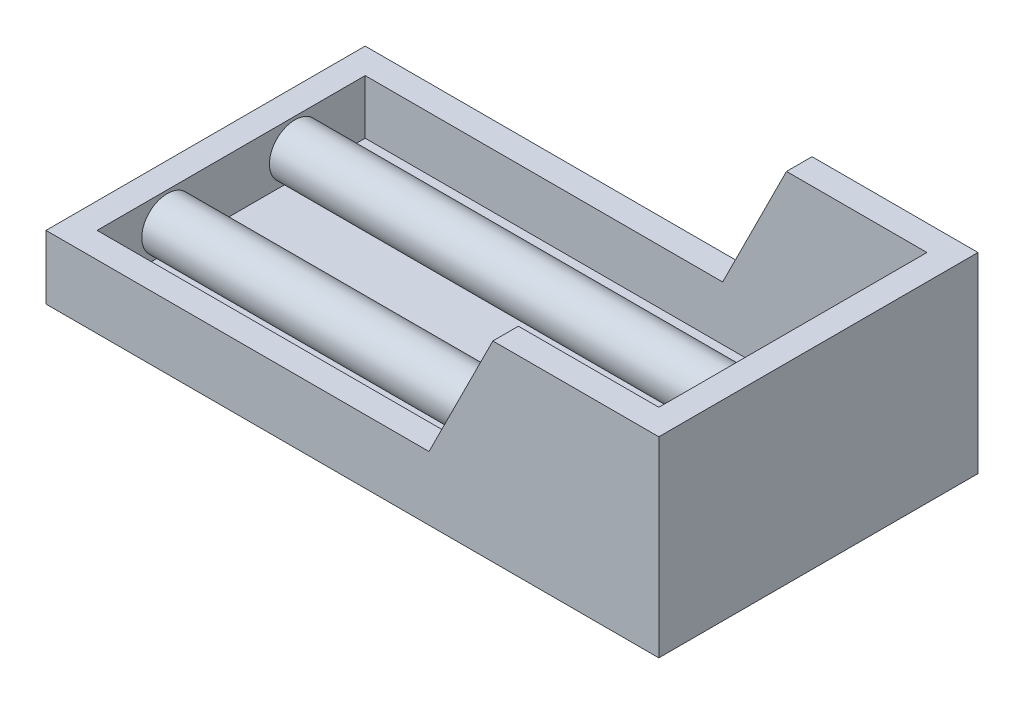
SolidWorks part; units mm, degrees
ref_plane "Front Plane" through (0, 0, 0) normal (0, 0, 1) x (1, 0, 0)
ref_plane "Top Plane" through (0, 0, 0) normal (0, 1, 0) x (1, 0, 0)
ref_plane "Right Plane" through (0, 0, 0) normal (1, 0, 0) x (0, 0, -1)
sketch "Sketch1" plane through (0, 0, 0) normal (0, 1, 0) x (1, 0, 0)
  line L1 (-10, 20) -> (38, 20)
  line L2 (-10, 20) -> (-10, -5)
  line L3 (-10, -5) -> (38, -5)
  line L4 (38, 20) -> (38, -5)
  point P0 (0, 0)
  dimension "D1" = 48
  dimension "D2" = 25
extrude "Boss-Extrude1" add sketch "Sketch1" along normal blind 15
sketch "Sketch2" plane through (0, 0, 5) normal (0, 0, 1) x (1, 0, 0)
  line L0 (25, 15) -> (20, 5)
  line L1 (-10, 15) -> (38, 15) construction
  line L2 (20, 5) -> (-10, 5)
  line L3 (-10, 15) -> (-10, 0) construction
  line L4 (-10, 5) -> (-10, 15)
  line L5 (-10, 15) -> (25, 15)
  dimension "D1" = 30
  dimension "D2" = 35
  dimension "D3" = 10
extrude "Cut-Extrude1" cut sketch "Sketch2" against normal through all
ref_plane "Plane1" through (0, 0.75, 0) normal (0, 1, 0) x (1, 0, 0)
sketch "Sketch4" plane through (0, 0.75, 0) normal (0, 1, 0) x (1, 0, 0)
  line L0 (-10, 20) -> (-10, -5) construction
  line L1 (-8, 18) -> (36, 18)
  line L2 (-8, 18) -> (-8, -3)
  line L3 (-8, -3) -> (36, -3)
  line L4 (36, 18) -> (36, -3)
  line L7 (-10, -5) -> (38, -5) construction
  point P0 (0, 0)
  dimension "D1" = 44
  dimension "D2" = 2
  dimension "D3" = 21
  dimension "2" = 2
extrude "Cut-Extrude2" cut sketch "Sketch4" along normal through all
sketch "Sketch5" plane through (-8, 0, 0) normal (1, 0, 0) x (0, 0, -1)
  line L1 (13.75, 0.75) -> (-13.75, 0.75) construction
  line L4 (7.5, 15) -> (7.5, 0.75) construction
  line L5 (-5, 15) -> (20, 15) construction
  line L6 (20, 15) -> (20, 0) construction
  circle A0 centre (12.5, 2.75) radius 2
  circle A2 centre (2.5, 2.75) radius 2
  point P17 (15, 2)
  dimension "D1" = 4
  dimension "D2" = 7.5
  dimension "D3" = 2
extrude "Boss-Extrude4" add sketch "Sketch5" along normal up to surface (44 mm away) separate body up to face at (36, 7.875, -7.5)
fillet "Fillet1" radius 1 1 edges at (36, 2.75, -10.5)
fillet "Fillet3" radius 1 1 edges at (36, 2.75, -0.5)
